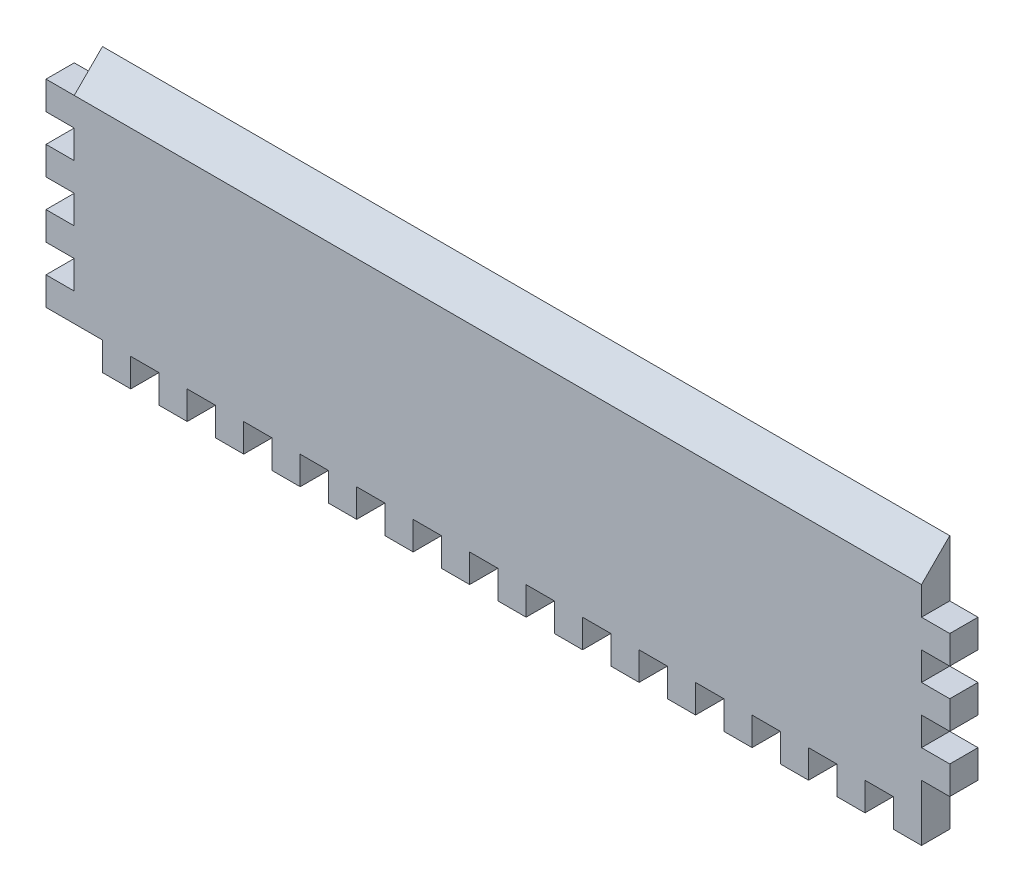
SolidWorks part; units mm, degrees
ref_plane "Front Plane" through (0, 0, 0) normal (0, 0, 1) x (1, 0, 0)
ref_plane "Top Plane" through (0, 0, 0) normal (0, 1, 0) x (1, 0, 0)
ref_plane "Right Plane" through (0, 0, 0) normal (1, 0, 0) x (0, 0, -1)
sketch "Sketch2" plane through (0, 0, 0) normal (0, 0, 1) x (1, 0, 0)
  line L1 (0, 0) -> (203.2, 0)
  line L2 (0, 0) -> (0, 57.15)
  line L3 (0, 57.15) -> (203.2, 57.15)
  line L4 (203.2, 0) -> (203.2, 57.15)
  dimension "D1" = 203.2
  dimension "D2" = 57.15
extrude "Boss-Extrude1" add sketch "Sketch2" along normal blind 6.35
sketch "Sketch3" plane through (0, 0, 0) normal (0, -1, 0) x (1, 0, 0)
  line L0 (0, 6.35) -> (203.2, 6.35) construction
  line L1 (0, 0) -> (12.7, 0)
  line L2 (0, 0) -> (0, 6.35)
  line L3 (0, 6.35) -> (12.7, 6.35)
  line L4 (12.7, 0) -> (12.7, 6.35)
extrude "Cut-Extrude1" cut sketch "Sketch3" against normal blind 6.35
sketch "Sketch5" plane through (0, 0, 0) normal (0, -1, 0) x (1, 0, 0)
  line L0 (12.7, 6.35) -> (203.2, 6.35) construction
  line L1 (19.05, 6.35) -> (25.4, 6.35)
  line L2 (19.05, 6.35) -> (19.05, 0)
  line L3 (19.05, 0) -> (25.4, 0)
  line L4 (25.4, 6.35) -> (25.4, 0)
  line L5 (12.7, 0) -> (203.2, 0) construction
extrude "Cut-Extrude2" cut sketch "Sketch5" against normal blind 6.35
pattern_linear "LPattern1" count 15 spacing 12.7 along (1, 0, 0) of "Cut-Extrude2"
sketch "Sketch6" plane through (203.2, 0, 0) normal (1, 0, 0) x (0, 0, -1)
  line L0 (0, 6.35) -> (0, 57.15) construction
  line L1 (-6.35, 6.35) -> (0, 6.35)
  line L2 (-6.35, 6.35) -> (-6.35, 12.7)
  line L3 (-6.35, 12.7) -> (0, 12.7)
  line L4 (0, 6.35) -> (0, 12.7)
extrude "Cut-Extrude3" cut sketch "Sketch6" against normal blind 6.35
sketch "Sketch7" plane through (203.2, 0, 0) normal (1, 0, 0) x (0, 0, -1)
  line L0 (-6.35, 12.7) -> (-6.35, 57.15) construction
  line L1 (-6.35, 19.05) -> (0, 19.05)
  line L2 (-6.35, 19.05) -> (-6.35, 25.4)
  line L3 (-6.35, 25.4) -> (0, 25.4)
  line L4 (0, 19.05) -> (0, 25.4)
  line L5 (0, 12.7) -> (0, 57.15) construction
extrude "Cut-Extrude4" cut sketch "Sketch7" against normal blind 6.35
pattern_linear "LPattern2" count 4 spacing 12.7 along (0, 1, 0) of "Cut-Extrude4"
sketch "Sketch8" plane through (203.2, 0, 0) normal (1, 0, 0) x (0, 0, -1)
  line L1 (-6.35, 50.8) -> (0, 50.8)
  line L2 (-6.35, 50.8) -> (-6.35, 57.15)
  line L3 (-6.35, 57.15) -> (0, 57.15)
  line L4 (0, 50.8) -> (0, 57.15)
extrude "Cut-Extrude5" cut sketch "Sketch8" against normal blind 6.35
sketch "Sketch9" plane through (0, 0, 0) normal (-1, 0, 0) x (0, 0, 1)
  line L0 (6.35, 57.15) -> (6.35, 6.35) construction
  line L1 (6.35, 12.7) -> (0, 12.7)
  line L2 (6.35, 12.7) -> (6.35, 19.05)
  line L3 (6.35, 19.05) -> (0, 19.05)
  line L4 (0, 12.7) -> (0, 19.05)
  line L5 (0, 57.15) -> (0, 6.35) construction
extrude "Cut-Extrude6" cut sketch "Sketch9" against normal blind 6.35
pattern_linear "LPattern3" count 4 spacing 12.7 along (0, 1, 0) of "Cut-Extrude6"
sketch "Sketch10" plane through (6.35, 0, 0) normal (-1, 0, 0) x (0, 0, 1)
  line L0 (6.35, 57.15) -> (6.35, 50.8)
  line L1 (6.35, 50.8) -> (0, 57.15)
  line L2 (0, 57.15) -> (6.35, 57.15)
extrude "Cut-Extrude7" cut sketch "Sketch10" against normal blind 190.5
